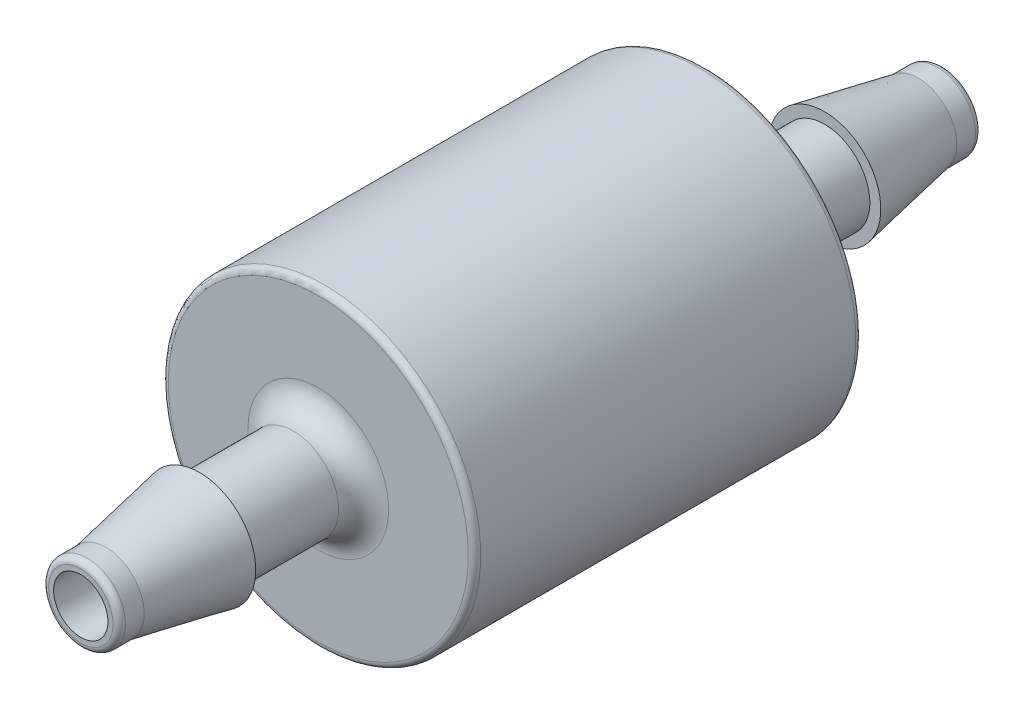
SolidWorks part; units mm, degrees
ref_plane "Front Plane" through (0, 0, 0) normal (0, 0, 1) x (1, 0, 0)
ref_plane "Top Plane" through (0, 0, 0) normal (0, 1, 0) x (1, 0, 0)
ref_plane "Right Plane" through (0, 0, 0) normal (1, 0, 0) x (0, 0, -1)
sketch "Sketch1" plane through (0, 0, 0) normal (1, 0, 0) x (0, 0, -1)
  line L0 (-17.526, 0) -> (17.526, 0) construction
  line L1 (17.526, 6.35) -> (17.526, -6.35) construction
  line L2 (-17.526, 1.1049) -> (-17.526, -1.1049) construction
  line L4 (-17.526, 1.5875) -> (-17.526, -1.5875) construction
  line L8 (-17.526, 6.35) -> (-17.526, -6.35) construction
  point P20 (-7.874, 0)
  point P21 (7.874, 0)
  dimension "OD" = 12.7
  dimension "Lg." = 35.052
  dimension "ID" = 2.2098
  dimension "L1" = 9.652
  dimension "L2" = 15.748
  dimension "L3" = 9.652
  dimension "Tube ID" = 3.175
sketch "Sketch2" plane through (0, 0, 0) normal (1, 0, 0) x (0, 0, -1)
  line L0 (17.526, 0) -> (-17.526, 0) construction
  line L1 (17.526, 6.35) -> (17.526, -6.35) construction
  line L2 (-17.526, 1.1049) -> (-17.526, -1.1049) construction
  line L3 (-17.526, 1.1049) -> (-17.526, 1.3081)
  line L4 (12.7, 1.8415) -> (8.89, 1.8415)
  line L5 (17.272, 1.5621) -> (16.51, 1.5621)
  line L6 (7.874, 2.8575) -> (7.874, 6.096)
  line L7 (17.526, 1.1049) -> (17.526, 1.3081)
  line L8 (-7.874, 2.8575) -> (-7.874, 6.096)
  line L9 (-7.62, 6.35) -> (7.62, 6.35)
  line L10 (12.7, 2.286) -> (12.7, 1.8415)
  line L11 (16.51, 1.5621) -> (12.7, 2.286)
  line L14 (0, 0) -> (0, 6.35) construction
  line L15 (-17.272, 1.5621) -> (-16.51, 1.5621)
  line L17 (-16.51, 1.5621) -> (-12.7, 2.286)
  line L18 (-12.7, 2.286) -> (-12.7, 1.8415)
  line L19 (-12.7, 1.8415) -> (-8.89, 1.8415)
  line L24 (-17.526, 1.1049) -> (17.526, 1.1049)
  arc A0 (7.874, 6.096) -> (7.62, 6.35) centre (7.62, 6.096) ccw
  arc A1 (-7.874, 6.096) -> (-7.62, 6.35) centre (-7.62, 6.096) cw
  arc A2 (-17.272, 1.5621) -> (-17.526, 1.3081) centre (-17.272, 1.3081) ccw
  arc A3 (17.272, 1.5621) -> (17.526, 1.3081) centre (17.272, 1.3081) cw
  arc A4 (-8.89, 1.8415) -> (-7.874, 2.8575) centre (-8.89, 2.8575) ccw
  arc A5 (8.89, 1.8415) -> (7.874, 2.8575) centre (8.89, 2.8575) cw
  dimension "D3" = 4.572
  dimension "D4" = 3.81
  dimension "D5" = 3.683
  dimension "R1" = 0.254
  dimension "R2" = 0.254
  dimension "R3" = 1.016
  dimension "D1" = 3.1242
  dimension "D2" = 1.016
revolve "Revolve1" add sketch "Sketch2" angle 360 mid plane about L0
sketch "SketchX" plane through (0, 0, 0) normal (1, 0, 0) x (0, 0, -1)
  line L10 (17.526, 1.1049) -> (-17.526, 1.1049) construction
  line L12 (-17.526, -1.1049) -> (17.526, -1.1049) construction
  line L13 (17.526, 1.1049) -> (-17.526, 1.1049)
  line L14 (-17.526, -1.1049) -> (17.526, -1.1049)
